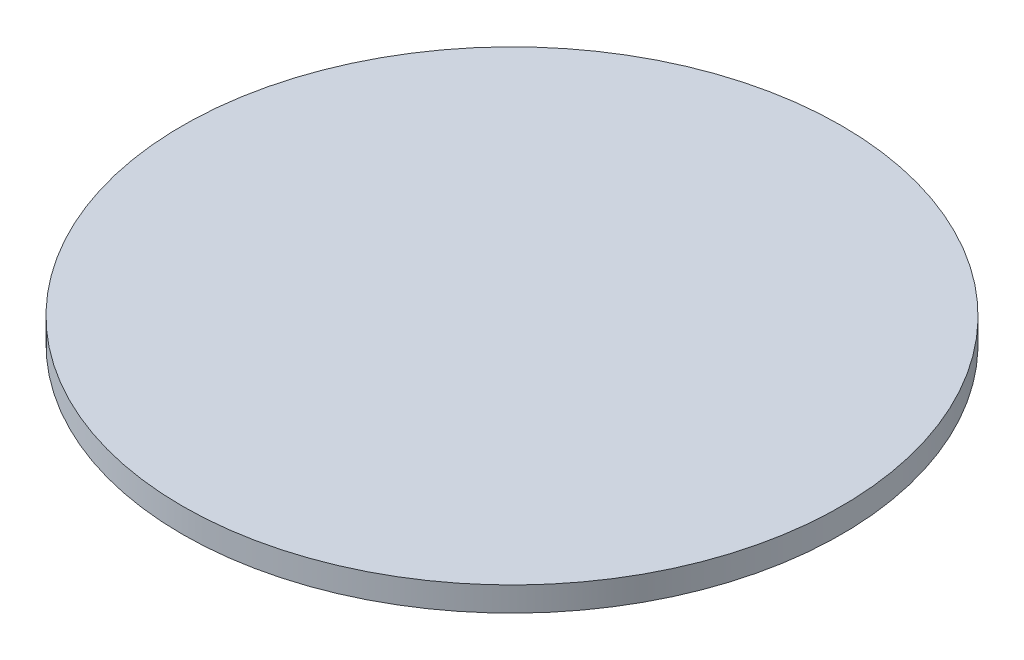
SolidWorks part; units mm, degrees
material "Glass"
ref_plane "Front Plane" through (0, 0, 0) normal (0, 0, 1) x (1, 0, 0)
ref_plane "Top Plane" through (0, 0, 0) normal (0, 1, 0) x (1, 0, 0)
ref_plane "Right Plane" through (0, 0, 0) normal (1, 0, 0) x (0, 0, -1)
sketch "Sketch1" plane through (0, 0, 0) normal (0, 1, 0) x (1, 0, 0)
  circle A0 centre (0, 0) radius 13.5
  dimension "D1" = 27
extrude "Boss-Extrude1" add sketch "Sketch1" along normal blind 1
